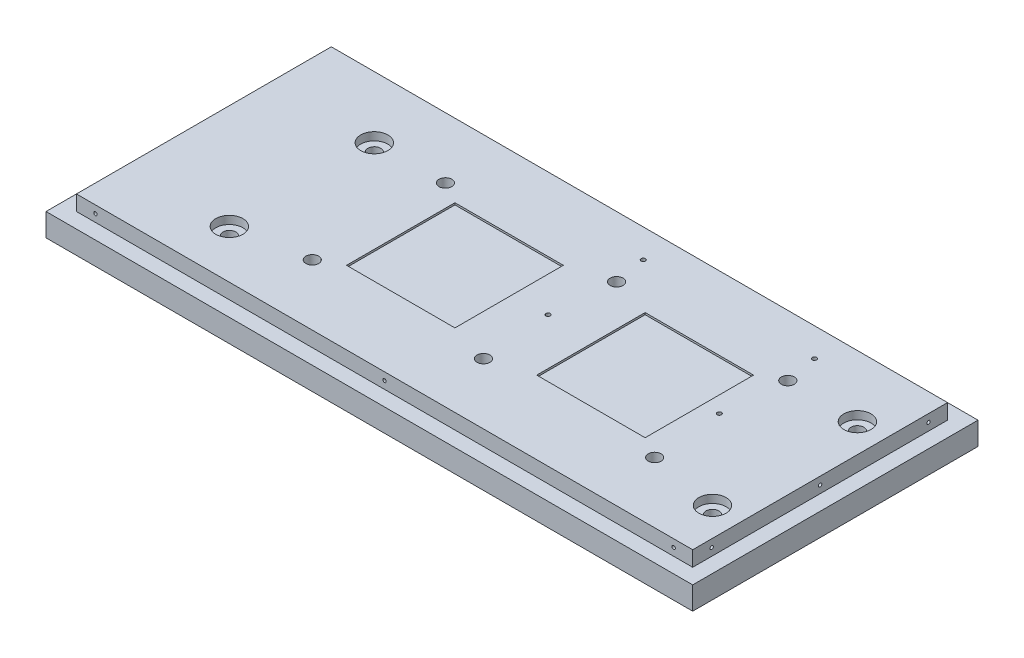
SolidWorks part; units mm, degrees
ref_plane "Front Plane" through (0, 0, 0) normal (0, 0, 1) x (1, 0, 0)
ref_plane "Top Plane" through (0, 0, 0) normal (0, 1, 0) x (1, 0, 0)
ref_plane "Right Plane" through (0, 0, 0) normal (1, 0, 0) x (0, 0, -1)
sketch "Sketch1" plane through (0, 0, 0) normal (0, 1, 0) x (1, 0, 0)
  line L1 (0, 0) -> (340, 0)
  line L2 (0, 0) -> (0, 150)
  line L3 (0, 150) -> (340, 150)
  line L4 (340, 0) -> (340, 150)
  dimension "D1" = 150
  dimension "D2" = 340
extrude "Boss-Extrude1" add sketch "Sketch1" along normal blind 20
hole_wizard "LaserCavityMountingHole_CBORE for 1/4 Socket Head Cap Screw1" positions "Sketch3" profile "Sketch4" counterbore size "1/4" standard "ANSI Inch" end condition through all
sketch "Sketch3" plane through (0, 0, 0) normal (0, -1, 0) x (-1, 0, 0)
  line L8 (-90, 120) -> (-290, 120)
  line L9 (-90, 120) -> (-90, 30)
  line L10 (-90, 30) -> (-290, 30)
  line L11 (-290, 120) -> (-290, 30)
  line L14 (-190, 120) -> (-190, 30) construction
  line L15 (0, 150) -> (0, 0) construction
  line L16 (-290, 75) -> (-90, 75) construction
  line L17 (-90, 75) -> (0, 75) construction
  line L18 (0, 150) -> (0, 0) construction
  line L21 (0, 75) -> (-340, 75) construction
  line L22 (-340, 0) -> (-340, 150) construction
  line L23 (-340, 0) -> (-340, 150) construction
  point P0 (-100, 40)
  point P2 (-190, 40)
  point P4 (-280, 40)
  point P6 (-280, 110)
  point P8 (-190, 110)
  point P10 (-100, 110)
  point P111 (-340, 75)
  dimension "D2" = 200
  dimension "D3" = 90
  dimension "D4" = 0
  dimension "D5" = 90
  dimension "D6" = 10
  dimension "D7" = 10
  dimension "D8" = 10
  dimension "D9" = 10
  dimension "D10" = 10
  dimension "D11" = 0
  dimension "D12" = 0
  dimension "D13" = 10
  dimension "D14" = 10
  dimension "D15" = 10
  dimension "D16" = 10
  dimension "D17" = 10
  dimension "D18" = 10
sketch "Sketch4" plane through (100, 0, -40) normal (1, 0, 0) x (0, 0, -1)
  line L0 (0, 0) -> (0, 20)
  line L1 (0, 20) -> (3.3782, 20)
  line L3 (3.3782, 20) -> (3.3782, 6.35)
  line L4 (3.3782, 6.35) -> (5.5562, 6.35)
  line L5 (5.5562, 6.35) -> (5.5562, 0)
  line L7 (5.5562, 0) -> (0, 0)
  line L11 (0, -6.35) -> (0, 107.95) construction
  dimension "Thru Hole Dia." = 6.7564
  dimension "Thru Hole Depth" = 20
  dimension "C'Bore Dia." = 11.1125
  dimension "C'Bore Depth" = 6.35
sketch "Sketch5" plane through (0, 20, 0) normal (0, 1, 0) x (1, 0, 0)
  line L0 (90, 30) -> (290, 30) construction
  line L1 (111.5, 103.5) -> (168.5, 103.5)
  line L2 (111.5, 103.5) -> (111.5, 46.5)
  line L3 (111.5, 46.5) -> (168.5, 46.5)
  line L4 (168.5, 103.5) -> (168.5, 46.5)
  line L5 (190, 120) -> (190, 30) construction
  line L11 (211.5, 103.5) -> (268.5, 103.5)
  line L12 (211.5, 103.5) -> (211.5, 46.5)
  line L13 (211.5, 46.5) -> (268.5, 46.5)
  line L14 (268.5, 103.5) -> (268.5, 46.5)
  point P4 (168.5, 75)
  point P7 (211.5, 75)
  point P8 (140, 46.5)
  point P11 (240, 46.5)
  dimension "D1" = 57
  dimension "D2" = 57
  dimension "D3" = 45
  dimension "D4" = 45
  dimension "D5" = 57
  dimension "D6" = 57
  dimension "D7" = 50
  dimension "D8" = 50
extrude "TEC_groove" cut sketch "Sketch5" against normal blind 1
sketch "Sketch6" plane through (0, 0, 0) normal (0, 0, 1) x (1, 0, 0)
  line L0 (340, 20) -> (340, 0) construction
  line L1 (0, 20) -> (340, 20)
  line L2 (0, 20) -> (0, 12)
  line L3 (0, 12) -> (340, 12)
  line L4 (340, 20) -> (340, 12)
  dimension "D1" = 8
extrude "Wall1" cut sketch "Sketch6" against normal blind 8
sketch "Sketch7" plane through (340, 0, 0) normal (1, 0, 0) x (0, 0, -1)
  line L0 (8, 12) -> (8, 20) construction
  line L1 (150, 20) -> (8, 20)
  line L2 (150, 20) -> (150, 12)
  line L3 (150, 12) -> (8, 12)
  line L4 (8, 20) -> (8, 12)
  dimension "D1" = 8
extrude "Wall2" cut sketch "Sketch7" against normal blind 8
sketch "Sketch9" plane through (0, 0, -150) normal (0, 0, -1) x (-1, 0, 0)
  line L0 (-332, 12) -> (-332, 20) construction
  line L1 (0, 20) -> (-332, 20)
  line L2 (0, 20) -> (0, 12)
  line L3 (0, 12) -> (-332, 12)
  line L4 (-332, 20) -> (-332, 12)
  dimension "D1" = 8
extrude "Wall3" cut sketch "Sketch9" against normal blind 8
sketch "Sketch10" plane through (0, 0, 0) normal (-1, 0, 0) x (0, 0, 1)
  line L1 (-142, 20) -> (-8, 20)
  line L2 (-142, 20) -> (-142, 12)
  line L3 (-142, 12) -> (-8, 12)
  line L4 (-8, 20) -> (-8, 12)
extrude "Wall4" cut sketch "Sketch10" against normal blind 8
hole_wizard "#2-56 Tapped Hole1" positions "Sketch13" profile "Sketch12" tap size "#2-56" standard "ANSI Inch"
sketch "Sketch13" plane through (0, 0, -8) normal (0, 0, 1) x (1, 0, 0)
  line L0 (8, 12) -> (8, 20) construction
  line L1 (8, 16) -> (332, 16) construction
  line L2 (332, 20) -> (332, 12) construction
  point P0 (18, 16)
  point P1 (322, 16)
  point P10 (170, 16)
  dimension "D1" = 10
  dimension "D2" = 0
  dimension "D3" = 10
  dimension "D4" = 0
sketch "Sketch12" plane through (18, 16, -8) normal (1, 0, 0) x (0, -1, 0)
  line L0 (0, 0) -> (0, 15.5342)
  line L1 (0, 15.5342) -> (0.889, 15)
  line L2 (0.889, 15) -> (0.889, 0)
  line L5 (0.889, 0) -> (0, 0)
  line L10 (0, 15.5342) -> (-0.889, 15) construction
  line L11 (0, -6.35) -> (0, 107.95) construction
  dimension "Tap Drill Dia." = 1.778
  dimension "Tap Drill Depth" = 15
  dimension "Drill Angle" = 118
cosmetic thread "Hole Thread1" parameters "D1"=12, "D2"=2.1844
cosmetic thread "Hole Thread2" parameters "D1"=12, "D2"=2.1844
cosmetic thread "Hole Thread13" parameters "D1"=12, "D2"=2.1844
hole_wizard "#2-56 Tapped Hole2" positions "3DSketch2" profile "Sketch15" tap size "#2-56" standard "ANSI Inch"
sketch3d "3DSketch2"
  line L0 (8, 20, -142) -> (8, 12, -142) construction
  line L1 (8, 16, -142) -> (8, 16, -8) construction
  line L2 (8, 12, -8) -> (8, 20, -8) construction
  line L3 (8, 20, -75) -> (8, 12, -75) construction
  line L4 (8, 20, -8) -> (8, 20, -142) construction
  line L5 (8, 12, -142) -> (8, 12, -8) construction
  point P0 (8, 16, -132)
  point P2 (8, 16, -18)
  point P11 (8, 16, -75)
  point P14 (8, 16, -75)
  point P16 (8, 16, -75)
  point P19 (8, 16, -75)
  point P21 (8, 16, -75)
  point P23 (8, 16, -91.6124)
  point P25 (8, 16, -75)
  point P28 (8, 16, -75)
  point P30 (8, 16, -75)
  point P46 (8, 16, -75)
  point P48 (8, 16, -75)
  point P50 (8, 16, -121.0214)
  point P52 (8, 16, -75)
  dimension "D1" = 10
  dimension "D2" = 10
  dimension "D3" = 0
  dimension "D4" = 0
  dimension "D5" = 0
  dimension "D6" = 0
sketch "Sketch15" plane through (8, 16, -132) normal (0, 1, 0) x (0, 0, 1)
  line L0 (0, 0) -> (0, 15.5342)
  line L1 (0, 15.5342) -> (0.889, 15)
  line L2 (0.889, 15) -> (0.889, 0)
  line L5 (0.889, 0) -> (0, 0)
  line L10 (0, 15.5342) -> (-0.889, 15) construction
  line L11 (0, -6.35) -> (0, 107.95) construction
  dimension "Tap Drill Dia." = 1.778
  dimension "Tap Drill Depth" = 15
  dimension "Drill Angle" = 118
cosmetic thread "Hole Thread3" parameters "D1"=12, "D2"=2.1844
cosmetic thread "Hole Thread4" parameters "D1"=12, "D2"=2.1844
cosmetic thread "Hole Thread40" parameters "D1"=12, "D2"=2.1844
sketch "Sketch16" plane through (8, 0, 0) normal (-1, 0, 0) x (0, 0, 1)
  line L0 (-142, 16) -> (-8, 16) construction
  line L1 (-142, 20) -> (-142, 12) construction
  line L2 (-8, 12) -> (-8, 20) construction
sketch "Sketch17" plane through (332, 0, 0) normal (1, 0, 0) x (0, 0, -1)
  line L0 (8, 16) -> (142, 16) construction
  line L1 (8, 20) -> (8, 12) construction
  line L2 (142, 20) -> (142, 12) construction
sketch "Sketch18" plane through (332, 0, 0) normal (1, 0, 0) x (0, 0, -1)
  line L0 (8, 16) -> (142, 16) construction
hole_wizard "#2-56 Tapped Hole3" positions "Sketch19" profile "Sketch20" tap size "#2-56" standard "ANSI Inch"
sketch "Sketch19" plane through (0, 0, -142) normal (0, 0, -1) x (-1, 0, 0)
  line L0 (-332, 16) -> (-8, 16) construction
  line L1 (-332, 20) -> (-332, 12) construction
  line L2 (-8, 20) -> (-8, 12) construction
  point P0 (-322, 16)
  point P2 (-18, 16)
  point P11 (-170, 16)
  dimension "D1" = 0
  dimension "D2" = 10
  dimension "D3" = 0
  dimension "D4" = 10
sketch "Sketch20" plane through (322, 16, -142) normal (1, 0, 0) x (0, 1, 0)
  line L0 (0, 0) -> (0, 15.5342)
  line L1 (0, 15.5342) -> (0.889, 15)
  line L2 (0.889, 15) -> (0.889, 0)
  line L5 (0.889, 0) -> (0, 0)
  line L10 (0, 15.5342) -> (-0.889, 15) construction
  line L11 (0, -6.35) -> (0, 107.95) construction
  dimension "Tap Drill Dia." = 1.778
  dimension "Tap Drill Depth" = 15
  dimension "Drill Angle" = 118
cosmetic thread "Hole Thread5" parameters "D1"=12, "D2"=2.1844
cosmetic thread "Hole Thread6" parameters "D1"=12, "D2"=2.1844
cosmetic thread "Hole Thread22" parameters "D1"=12, "D2"=2.1844
hole_wizard "ElectronicBoardMounting" positions "Sketch21" profile "Sketch22" tap size "#4-40" standard "ANSI Inch"
sketch "Sketch21" plane through (0, 20, 0) normal (0, 1, 0) x (1, 0, 0)
  line L1 (182, 132) -> (282, 132)
  line L2 (182, 132) -> (182, 72)
  line L3 (182, 72) -> (282, 72)
  line L4 (282, 132) -> (282, 72)
  line L8 (332, 142) -> (332, 8) construction
  line L9 (8, 142) -> (332, 142) construction
  point P0 (187, 127)
  point P2 (277, 127)
  point P4 (277, 77)
  point P6 (187, 77)
  point P108 (232, 132)
  dimension "D1" = 60
  dimension "D2" = 100
  dimension "D3" = 100
  dimension "D4" = 10
  dimension "D5" = 5
  dimension "D6" = 5
  dimension "D7" = 5
  dimension "D8" = 5
  dimension "D9" = 5
  dimension "D10" = 5
  dimension "D11" = 5
  dimension "D12" = 5
sketch "Sketch22" plane through (187, 20, -127) normal (1, 0, 0) x (0, 0, 1)
  line L0 (0, 0) -> (0, 20.6792)
  line L1 (0, 20.6792) -> (1.1303, 20)
  line L2 (1.1303, 20) -> (1.1303, 0)
  line L5 (1.1303, 0) -> (0, 0)
  line L10 (0, 20.6792) -> (-1.1303, 20) construction
  line L11 (0, -6.35) -> (0, 107.95) construction
  dimension "Tap Drill Dia." = 2.2606
  dimension "Tap Drill Depth" = 20
  dimension "Drill Angle" = 118
cosmetic thread "Hole Thread7" parameters "D1"=20, "D2"=2.8448
cosmetic thread "Hole Thread8" parameters "D1"=20, "D2"=2.8448
cosmetic thread "Hole Thread9" parameters "D1"=20, "D2"=2.8448
cosmetic thread "Hole Thread10" parameters "D1"=20, "D2"=2.8448
hole_wizard "#2-56 Tapped Hole4" positions "Sketch23" profile "Sketch24" tap size "#2-56" standard "ANSI Inch"
sketch "Sketch23" plane through (332, 0, 0) normal (1, 0, 0) x (0, 0, -1)
  line L0 (142, 16) -> (8, 16) construction
  line L1 (8, 20) -> (8, 12) construction
  line L2 (142, 20) -> (142, 12) construction
  point P0 (18, 16)
  point P4 (132, 16)
  point P11 (75, 16)
  dimension "D1" = 10
  dimension "D2" = 10
sketch "Sketch24" plane through (332, 16, -18) normal (0, 1, 0) x (0, 0, -1)
  line L0 (0, 0) -> (0, 15.5342)
  line L1 (0, 15.5342) -> (0.889, 15)
  line L2 (0.889, 15) -> (0.889, 0)
  line L5 (0.889, 0) -> (0, 0)
  line L10 (0, 15.5342) -> (-0.889, 15) construction
  line L11 (0, -6.35) -> (0, 107.95) construction
  dimension "Tap Drill Dia." = 1.778
  dimension "Tap Drill Depth" = 15
  dimension "Drill Angle" = 118
cosmetic thread "Hole Thread11" parameters "D1"=12, "D2"=2.1844
cosmetic thread "Hole Thread12" parameters "D1"=12, "D2"=2.1844
cosmetic thread "Hole Thread23" parameters "D1"=12, "D2"=2.1844
hole_wizard "OpticalTableMountingHoles_CBORE for 1/4 Binding Head Machine Screw1" positions "Sketch25" profile "Sketch26" counterbore size "1/4" standard "ANSI Inch"
sketch "Sketch25" plane through (0, 20, 0) normal (0, 1, 0) x (1, 0, 0)
  line L0 (332, 8) -> (332, 142) construction
  line L1 (332, 8) -> (8, 8) construction
  point P0 (63, 109.6)
  point P2 (317, 109.6)
  point P4 (317, 33.4)
  point P6 (63, 33.4)
  dimension "D1" = 15
  dimension "D2" = 25.4
  dimension "D3" = 76.2
  dimension "D4" = 0
  dimension "D5" = 254
  dimension "D6" = 0
  dimension "D7" = 254
  dimension "D8" = 76.2
sketch "Sketch26" plane through (63, 20, -109.6) normal (1, 0, 0) x (0, 0, 1)
  line L0 (0, 0) -> (0, 22.0298)
  line L1 (0, 22.0298) -> (3.3782, 20)
  line L2 (3.3782, 20) -> (3.3782, 4.191)
  line L3 (3.3782, 4.191) -> (7.1437, 4.191)
  line L4 (7.1437, 4.191) -> (7.1437, 0)
  line L5 (7.1437, 0) -> (0, 0)
  line L10 (0, 22.0298) -> (-3.3782, 20) construction
  line L11 (0, -6.35) -> (0, 107.95) construction
  dimension "Hole Dia." = 6.7564
  dimension "Hole Depth" = 20
  dimension "C'Bore Dia." = 14.2875
  dimension "C'Bore Depth" = 4.191
  dimension "Drill Angle" = 118
